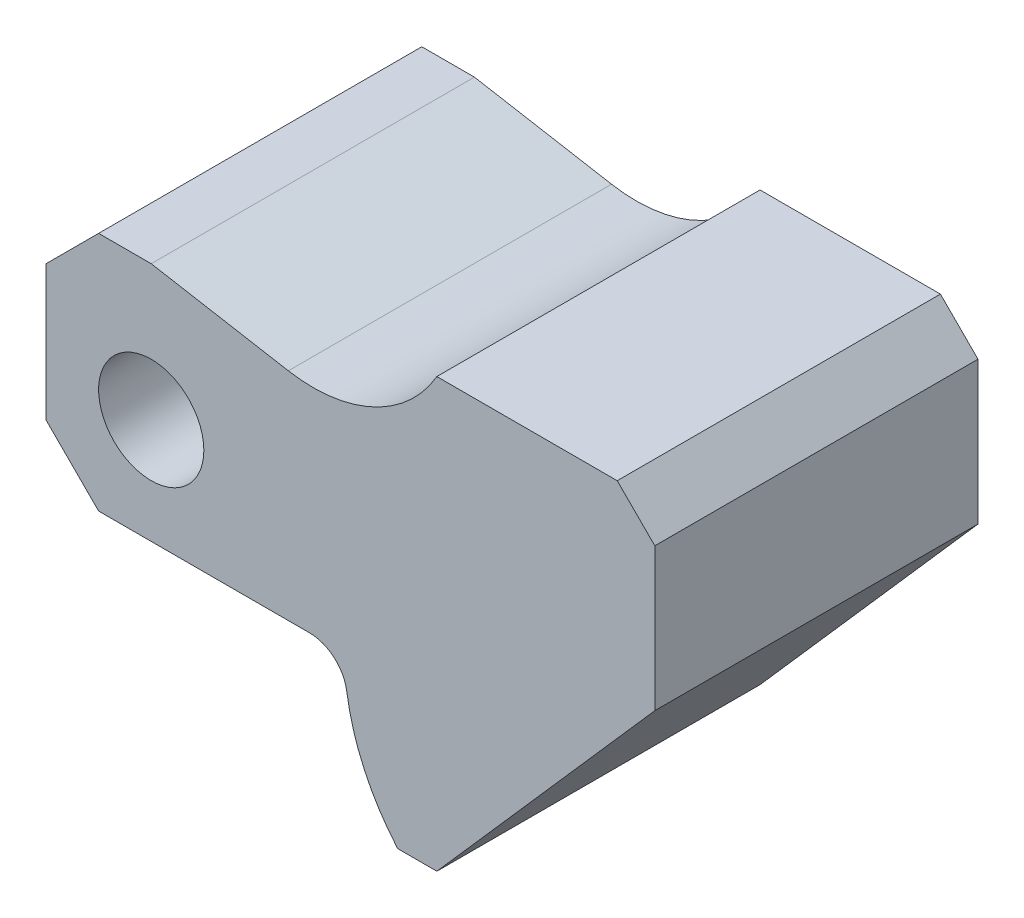
SolidWorks part; units mm, degrees
material "AISI 1020"
ref_plane "Front Plane" through (0, 0, 0) normal (0, 0, 1) x (1, 0, 0)
ref_plane "Top Plane" through (0, 0, 0) normal (0, 1, 0) x (1, 0, 0)
ref_plane "Right Plane" through (0, 0, 0) normal (1, 0, 0) x (0, 0, -1)
sketch "Sketch1" plane through (0, 0, 0) normal (0, 0, 1) x (1, 0, 0)
  line L0 (0, -32) -> (81, -32) construction
  line L1 (0, 0) -> (14, 0)
  line L2 (0, 0) -> (0, -32)
  line L3 (0, -32) -> (14, -32)
  line L4 (14, 0) -> (14, -32)
  line L5 (81, -32) -> (81, 6) construction
  line L6 (81.0032, -51) -> (52.0032, -51) construction
  line L7 (52, 6) -> (81, 6)
  line L8 (52, 6) -> (52, -18)
  line L9 (52, -18) -> (81, -18)
  line L10 (81, 6) -> (81, -18)
  line L11 (14, -32) -> (14, -51) construction
  line L12 (14, -51) -> (81.0032, -51) construction
  line L13 (81.0032, -51) -> (52.0032, -51) construction
  line L14 (81, -18) -> (52.0032, -51)
  line L15 (14, -32) -> (39.6983, -32)
  line L16 (14, 0) -> (32.2431, -3.2167)
  line L17 (46.7894, -51) -> (52.0032, -51)
  line L18 (14, -32) -> (39.6983, -32)
  line L19 (14, -32) -> (14, -18) construction
  arc A0 (39.6983, -32) -> (46.7894, -51) centre (68.6983, -32) ccw
  circle A1 centre (14, -18) radius 7
  arc A2 (32.2431, -3.2167) -> (52, 6) centre (35.5424, 15.4946) ccw
  point P18 (-24.6795, -34.913)
  dimension "D7" = 38
  dimension "D8" = 19
  dimension "D4" = 81
  dimension "D10" = 43.9297
  dimension "D12" = 29
  dimension "D13" = 14
  dimension "D14" = 14
  dimension "D3" = 19
  dimension "D1" = 14
  dimension "D2" = 32
  dimension "D5" = 29
  dimension "D6" = 24
  dimension "D9" = 29
  dimension "D11" = 190
  dimension "D15" = 57
extrude "Boss-Extrude1" add sketch "Sketch1" along normal blind 43 contours A2 L16 L4 L15 A0 L17 L14 L9 L8 | L4 L1 L2 L3 | L10 L7 L8 L9
chamfer "Chamfer1" distance 7 angle 45 1 edges at (0, 0, 21.5)
chamfer "Chamfer2" distance 7 angle 45 1 edges at (0, -32, 21.5)
chamfer "Chamfer3" distance 5 angle 45 1 edges at (81, 6, 21.5)
fillet "Fillet1" radius 5 1 edges at (39.6983, -32, 21.5)
